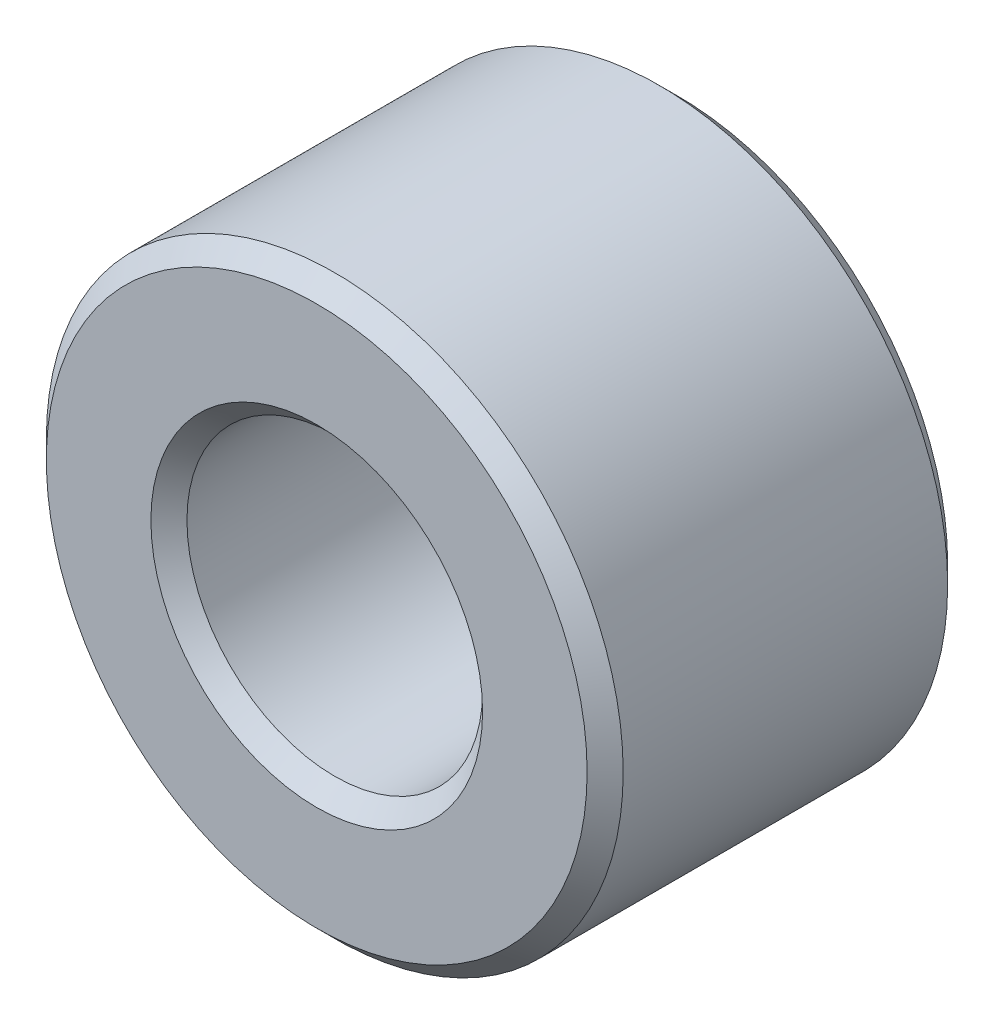
SolidWorks part; units mm, degrees
ref_plane "Front Plane" through (0, 0, 0) normal (0, 0, 1) x (1, 0, 0)
ref_plane "Top Plane" through (0, 0, 0) normal (0, 1, 0) x (1, 0, 0)
ref_plane "Right Plane" through (0, 0, 0) normal (1, 0, 0) x (0, 0, -1)
sketch "Sketch1" plane through (0, 0, 0) normal (0, 0, 1) x (1, 0, 0)
  circle A0 centre (0, 0) radius 4
  circle A1 centre (0, 0) radius 2.05
  dimension "OD" = 8
  dimension "ID" = 4.1
extrude "Extrude1" add sketch "Sketch1" along normal blind 5
chamfer "Chamfer2" distance 0.25 angle 45 4 edges at (4, 0, 0) (2.05, 0, 0) (4, 0, 5) (2.05, 0, 5)
